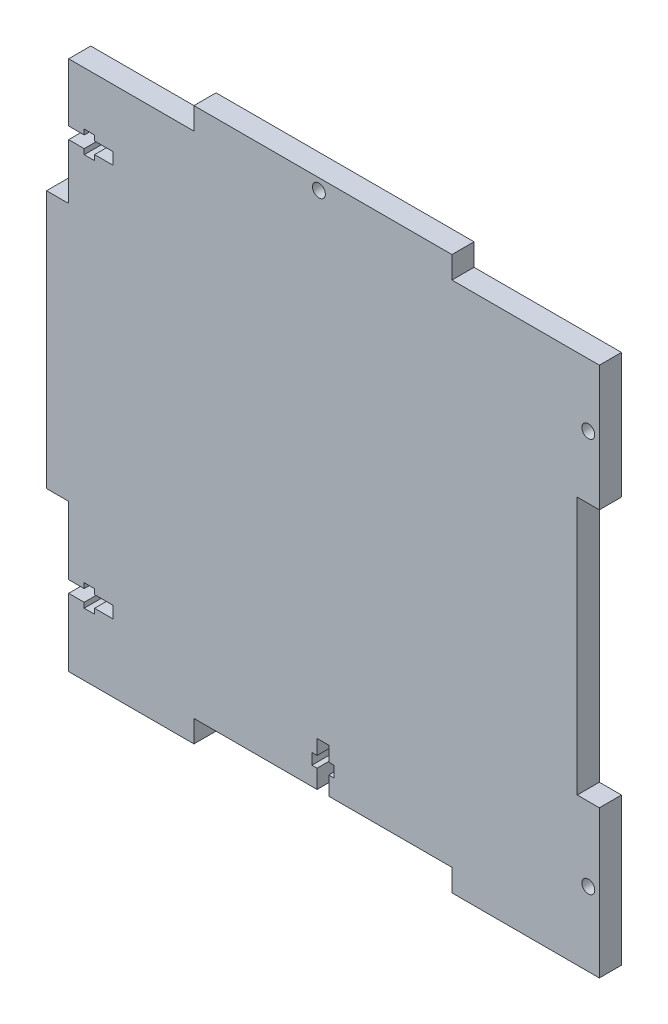
SolidWorks part; units mm, degrees
ref_plane "Front Plane" through (0, 0, 0) normal (0, 0, 1) x (1, 0, 0)
ref_plane "Top Plane" through (0, 0, 0) normal (0, 1, 0) x (1, 0, 0)
ref_plane "Right Plane" through (0, 0, 0) normal (1, 0, 0) x (0, 0, -1)
sketch "Sketch1" plane through (0, 0, 0) normal (0, 0, 1) x (1, 0, 0)
  line L0 (-38, 72) -> (-38, 78)
  line L1 (-72, -72) -> (72, -72)
  line L2 (-72, -72) -> (-72, 72)
  line L3 (-72, 72) -> (72, 72)
  line L4 (72, -72) -> (72, 72)
  line L5 (-72, -72) -> (72, 72) construction
  line L6 (-72, 72) -> (72, -72) construction
  line L7 (-38, 78) -> (32, 78)
  line L8 (32, 78) -> (32, 72)
  line L9 (-38, -72) -> (-38, -66)
  line L10 (-38, -66) -> (32, -66)
  line L11 (32, -66) -> (32, -72)
  line L12 (-72, 38) -> (-78, 38)
  line L13 (-78, 38) -> (-78, -32)
  line L14 (-78, -32) -> (-72, -32)
  line L15 (72, 38) -> (66, 38)
  line L16 (66, 38) -> (66, -32)
  line L17 (66, -32) -> (72, -32)
  line L18 (0, 108.2426) -> (0, -112.6743) construction
  line L19 (-72, 56.2) -> (-60, 56.2)
  line L24 (-72, -50.4) -> (-60, -50.4)
  line L25 (-72, -50.4) -> (-72, -53.6)
  line L26 (-72, -53.6) -> (-60, -53.6)
  line L27 (-60, -50.4) -> (-60, -53.6)
  line L28 (-67.7819, -49) -> (-64.967, -49)
  line L29 (-67.7819, -49) -> (-67.7819, -55)
  line L30 (-67.7819, -55) -> (-64.967, -55)
  line L31 (-64.967, -49) -> (-64.967, -55)
  line L32 (-72, 53) -> (-60, 53)
  line L33 (-60, 56.2) -> (-60, 53)
  line L34 (-67.7728, 57.6) -> (-64.958, 57.6)
  line L35 (-67.7728, 57.6) -> (-67.7728, 51.5685)
  line L36 (-67.7728, 51.5685) -> (-64.958, 51.5685)
  line L37 (-64.958, 57.6) -> (-64.958, 51.5685)
  line L39 (-4.6, -54) -> (-1.4, -54)
  line L40 (-4.6, -54) -> (-4.6, -66)
  line L41 (-4.6, -66) -> (-1.4, -66)
  line L42 (-1.4, -54) -> (-1.4, -66)
  line L43 (-6, -58) -> (0, -58)
  line L44 (-6, -58) -> (-6, -61)
  line L45 (-6, -61) -> (0, -61)
  line L46 (0, -58) -> (0, -61)
  circle A0 centre (69, 55) radius 1.75
  circle A3 centre (69, -52) radius 1.75
  circle A4 centre (-4.09, 75) radius 1.75
  point P0 (0, 0)
  dimension "D16" = 3.5
  dimension "D20" = 12
  dimension "D19" = 3.2
  dimension "D30" = 3
  dimension "D31" = 76.09
  dimension "D2" = 6
  dimension "D3" = 40
  dimension "D4" = 40
  dimension "D5" = 6
  dimension "D6" = 40
  dimension "D7" = 150
  dimension "D8" = 6
  dimension "D9" = 6
  dimension "D10" = 40
  dimension "D11" = 40
  dimension "D12" = 6
  dimension "D13" = 40
  dimension "D14" = 40
  dimension "D15" = 150
  dimension "D17" = 3
  dimension "D18" = 17
  dimension "D21" = 18.4
  dimension "D22" = 3
  dimension "D23" = 6
  dimension "D24" = 20
  dimension "D25" = 1.4
  dimension "D26" = 15
  dimension "D27" = 1.4
  dimension "D28" = 3.2
  dimension "D29" = 12
  dimension "D32" = 40
  dimension "D33" = 3.2
  dimension "D34" = 12
  dimension "D35" = 3
  dimension "D36" = 1.4
  dimension "D37" = 6
  dimension "D38" = 5
  dimension "D39" = 33.4
  dimension "D40" = 0
extrude "Boss-Extrude2" add sketch "Sketch1" along normal blind 6 contours L17 L16 L15 L4 L3 L2 L1 L9 L10 L11 | L13 L14 L2 L12 | L8 L7 L0 L3
sketch "Sketch3" plane through (0, 0, 0) normal (0, 0, -1) x (-1, 0, 0)
  circle A0 centre (2.0753, 36.4917) radius 3
  circle A1 centre (29, -0.5) radius 3
  circle A2 centre (-16.5, -0.5) radius 3.0671
equation "\"`2\"=15.927"
